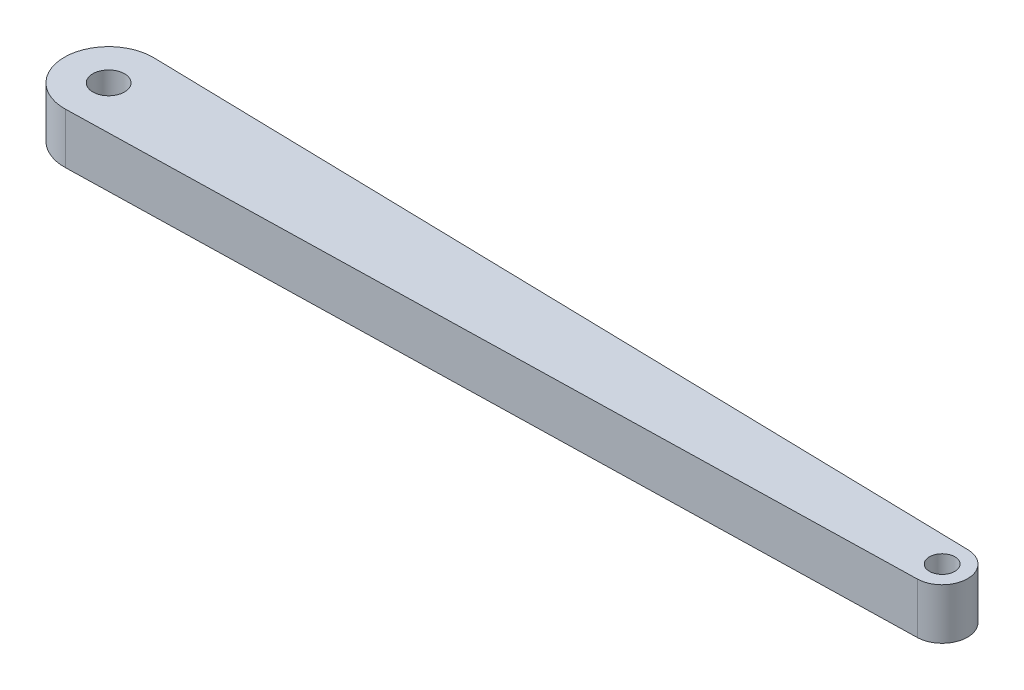
SolidWorks part; units mm, degrees
ref_plane "Front Plane" through (0, 0, 0) normal (0, 0, 1) x (1, 0, 0)
ref_plane "Top Plane" through (0, 0, 0) normal (0, 1, 0) x (1, 0, 0)
ref_plane "Right Plane" through (0, 0, 0) normal (1, 0, 0) x (0, 0, -1)
sketch "Sketch1" plane through (0, 0, 0) normal (0, 1, 0) x (1, 0, 0)
  line L0 (1.597, 69.9818) -> (1315.9125, 39.9896)
  line L1 (0, 0) -> (1315, 0) construction
  line L2 (1.597, -69.9818) -> (1315.9125, -39.9896)
  circle A0 centre (0, 0) radius 25
  arc A1 (1.597, 69.9818) -> (1.597, -69.9818) centre (0, 0) ccw
  circle A2 centre (1315, 0) radius 20
  arc A3 (1315.9125, -39.9896) -> (1315.9125, 39.9896) centre (1315, 0) ccw
  dimension "D1" = 50
  dimension "D2" = 140
  dimension "D3" = 40
  dimension "D4" = 80
  dimension "D5" = 1315
extrude "Boss-Extrude1" add sketch "Sketch1" along normal mid plane 80
